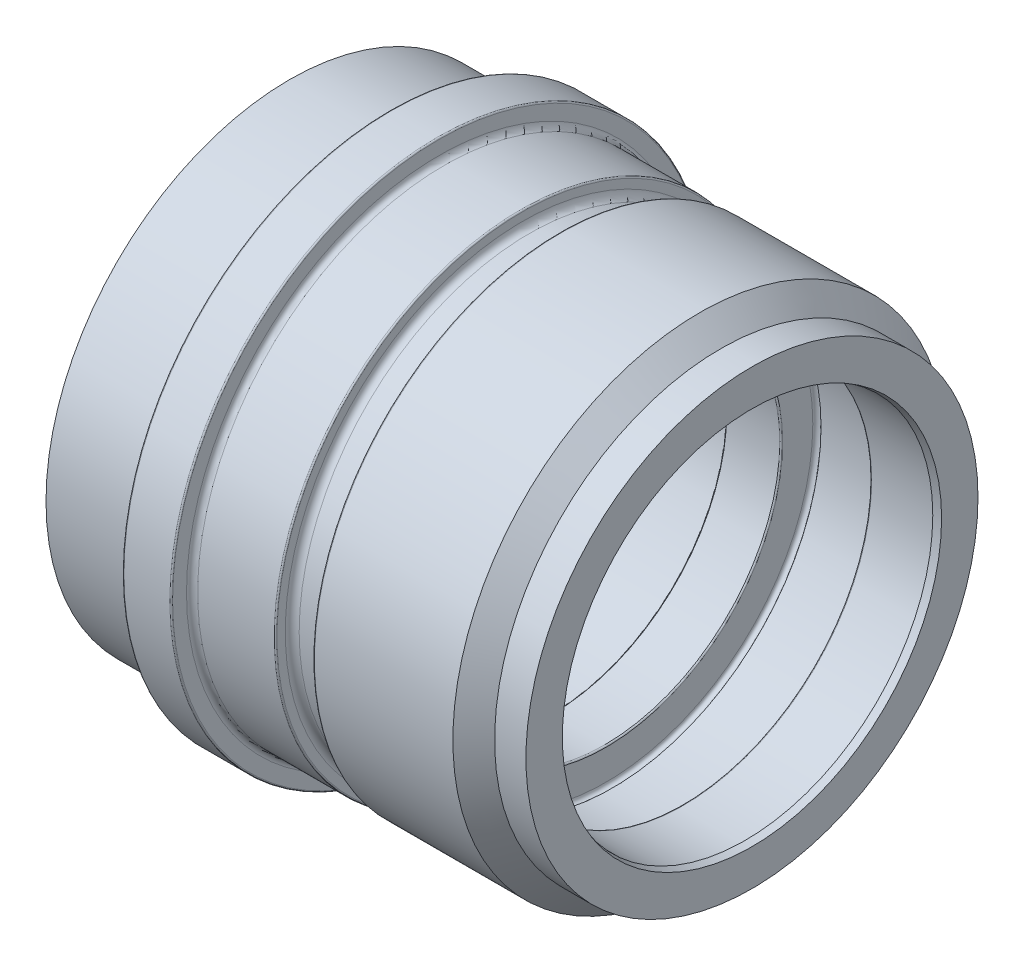
SolidWorks part; units mm, degrees
ref_plane "Front" through (0, 0, 0) normal (0, 0, 1) x (1, 0, 0)
ref_plane "Top" through (0, 0, 0) normal (0, 1, 0) x (1, 0, 0)
ref_plane "Right" through (0, 0, 0) normal (1, 0, 0) x (0, 0, -1)
sketch "Sketch1" plane through (0, 0, 0) normal (0, 0, 1) x (1, 0, 0)
  line L0 (0, 0) -> (-93.4733, 0) construction
  line L1 (0, -13.5831) -> (0, 60.7666) construction
  line L2 (0, 36.3) -> (0, 38.3)
  line L3 (-0.2, 38.5) -> (-6.8, 38.5)
  line L4 (-7, 38.3) -> (-7, 35.2)
  line L5 (-7.2, 35) -> (-21.5, 35)
  line L6 (-21.5, 35) -> (-21.5, 30.5774)
  line L7 (-21.5, 30.5774) -> (-20.5, 30)
  line L8 (-20.5, 30) -> (-14.8, 30)
  line L9 (-14, 29.2) -> (-14, 25.5)
  line L10 (-14, 25.5) -> (-9.2, 25.5)
  line L11 (-9, 25.7) -> (-9, 27.3)
  line L12 (-8.8, 27.5) -> (15.8, 27.5)
  line L13 (16, 27.3) -> (16, 25.4)
  line L14 (16.2, 25.2) -> (23.8, 25.2)
  line L15 (24, 25.4) -> (24, 29.75)
  line L16 (24.933, 30) -> (34.6, 30)
  line L17 (35, 29.6) -> (35, 27.2)
  line L18 (35.2, 27) -> (44, 27)
  line L19 (44, 27) -> (45, 27.2679)
  line L20 (45, 27.2679) -> (45, 32.5)
  line L21 (45, 32.5) -> (40.5, 32.5)
  line L22 (40.5, 32.5) -> (37.5, 35.5)
  line L23 (37.5, 35.5) -> (17.6, 35.5)
  line L24 (17.4, 35.3) -> (17.4, 34.1)
  line L25 (16.4, 33.1) -> (13, 33.1)
  line L26 (12, 34.1) -> (12, 35.3)
  line L27 (11.8, 35.5) -> (0.8, 35.5)
  arc A0 (17.6, 35.5) -> (17.4, 35.3) centre (17.6, 35.3) ccw
  arc A1 (12, 35.3) -> (11.8, 35.5) centre (11.8, 35.3) ccw
  arc A4 (0, 36.3) -> (0.8, 35.5) centre (0.8, 36.3) ccw
  arc A5 (0, 38.3) -> (-0.2, 38.5) centre (-0.2, 38.3) ccw
  arc A6 (-6.8, 38.5) -> (-7, 38.3) centre (-6.8, 38.3) ccw
  arc A7 (-7, 35.2) -> (-7.2, 35) centre (-7.2, 35.2) cw
  arc A8 (16, 25.4) -> (16.2, 25.2) centre (16.2, 25.4) ccw
  arc A9 (15.8, 27.5) -> (16, 27.3) centre (15.8, 27.3) cw
  arc A10 (-9, 27.3) -> (-8.8, 27.5) centre (-8.8, 27.3) cw
  arc A11 (-9.2, 25.5) -> (-9, 25.7) centre (-9.2, 25.7) ccw
  arc A12 (35, 27.2) -> (35.2, 27) centre (35.2, 27.2) ccw
  arc A13 (23.8, 25.2) -> (24, 25.4) centre (23.8, 25.4) ccw
  arc A14 (34.6, 30) -> (35, 29.6) centre (34.6, 29.6) cw
  arc A15 (24, 29.75) -> (24.933, 30) centre (24.5, 29.75) cw
  arc A16 (-14.8, 30) -> (-14, 29.2) centre (-14.8, 29.2) cw
  arc A17 (13, 33.1) -> (12, 34.1) centre (13, 34.1) cw
  arc A18 (17.4, 34.1) -> (16.4, 33.1) centre (16.4, 34.1) cw
  point P41 (0, 35.5)
  point P44 (0, 38.5)
  dimension "D28" = 0.2
  dimension "D30" = 0.8
  dimension "D31" = 0.2
  dimension "D32" = 0.2
  dimension "D33" = 0.2
  dimension "D34" = 0.4
  dimension "D35" = 0.8
  dimension "D37" = 0.5
  dimension "D38" = 0.25
  dimension "D39" = 1
  dimension "D2" = 66.5
  dimension "D3" = 7
  dimension "D4" = 51
  dimension "D5" = 55
  dimension "D6" = 60
  dimension "D7" = 11
  dimension "D8" = 21
  dimension "D9" = 54
  dimension "D10" = 25
  dimension "D11" = 7.5
  dimension "D12" = 1
  dimension "D13" = 30
  dimension "D14" = 77
  dimension "D15" = 70
  dimension "D16" = 71
  dimension "D17" = 66.2
  dimension "D18" = 5.4
  dimension "D19" = 33
  dimension "D20" = 60
  dimension "D21" = 65
  dimension "D22" = 15
  dimension "D23" = 1
  dimension "D24" = 45
  dimension "D25" = 4.5
  dimension "D26" = 54
  dimension "D27" = 45
  dimension "D36" = 50.4
revolve "Base-Revolve" add sketch "Sketch1" angle 360 about L0
